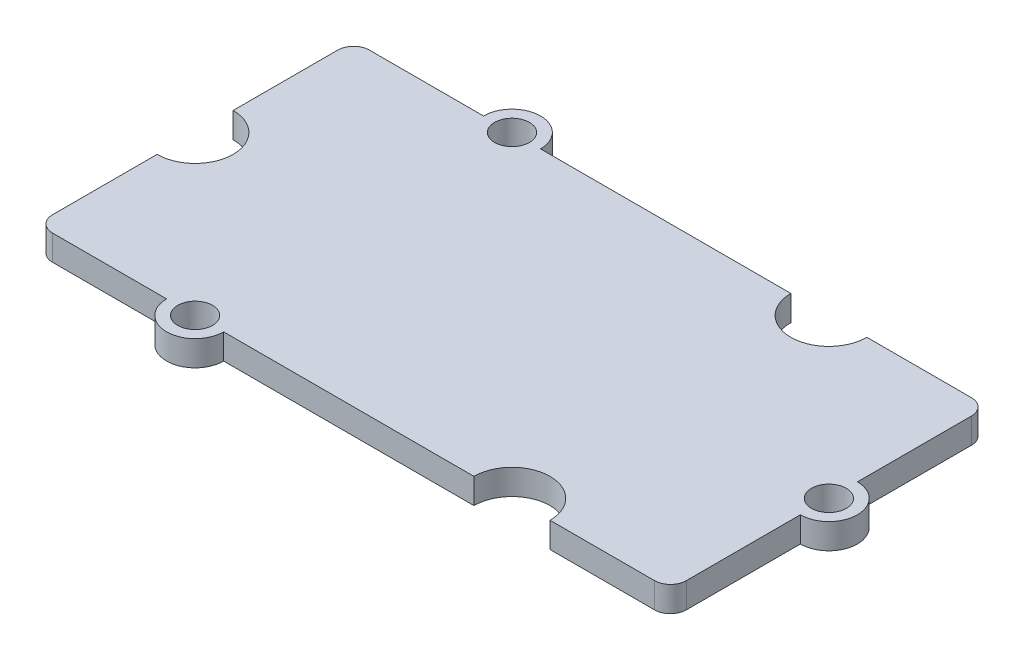
SolidWorks part; units mm, degrees
ref_plane "Plan de face" through (0, 0, 0) normal (0, 0, 1) x (1, 0, 0)
ref_plane "Plan de dessus" through (0, 0, 0) normal (0, 1, 0) x (1, 0, 0)
ref_plane "Plan de droite" through (0, 0, 0) normal (1, 0, 0) x (0, 0, -1)
sketch "Esquisse1" plane through (0, 0, 0) normal (0, 1, 0) x (1, 0, 0)
  line L1 (-19, -10) -> (19, -10)
  line L2 (-20, -9) -> (-20, 9)
  line L3 (-19, 10) -> (19, 10)
  line L4 (20, -9) -> (20, 9)
  line L5 (-20, -10) -> (20, 10) construction
  line L6 (-20, 10) -> (20, -10) construction
  circle A0 centre (-10, 10) radius 1.8
  circle A1 centre (-10, -10) radius 1.8
  circle A2 centre (-20, 0) radius 2.4
  circle A3 centre (10, 10) radius 2.4
  circle A4 centre (-10, 10) radius 1.1
  arc A5 (19, 10) -> (20, 9) centre (19, 9) cw
  circle A6 centre (-10, -10) radius 1.1
  arc A7 (-19, -10) -> (-20, -9) centre (-19, -9) cw
  arc A8 (19, -10) -> (20, -9) centre (19, -9) ccw
  arc A9 (-20, 9) -> (-19, 10) centre (-19, 9) cw
  circle A10 centre (10, -10) radius 2.4
  circle A11 centre (20, 0) radius 1.8
  circle A12 centre (20, 0) radius 1.1
  point P0 (0, 0)
  dimension "D2" = 1
  dimension "D3" = 4.8
  dimension "D4" = 2.2
  dimension "D5" = 3.6
  dimension "D7" = 10
  dimension "D8" = 30
  dimension "D1" = 40
  dimension "D6" = 20
extrude "Boss.-Extru.1" add sketch "Esquisse1" along normal blind 1.6 contours A9 L2 A2 A7 L1 A1 A8 L4 A3 A5 L3 A0 | A4 L3 A0 | A4 L3 A0 | A6 L1 A1 | A6 L1 A1 | A12 L4 A11 | A12 L4 A11
